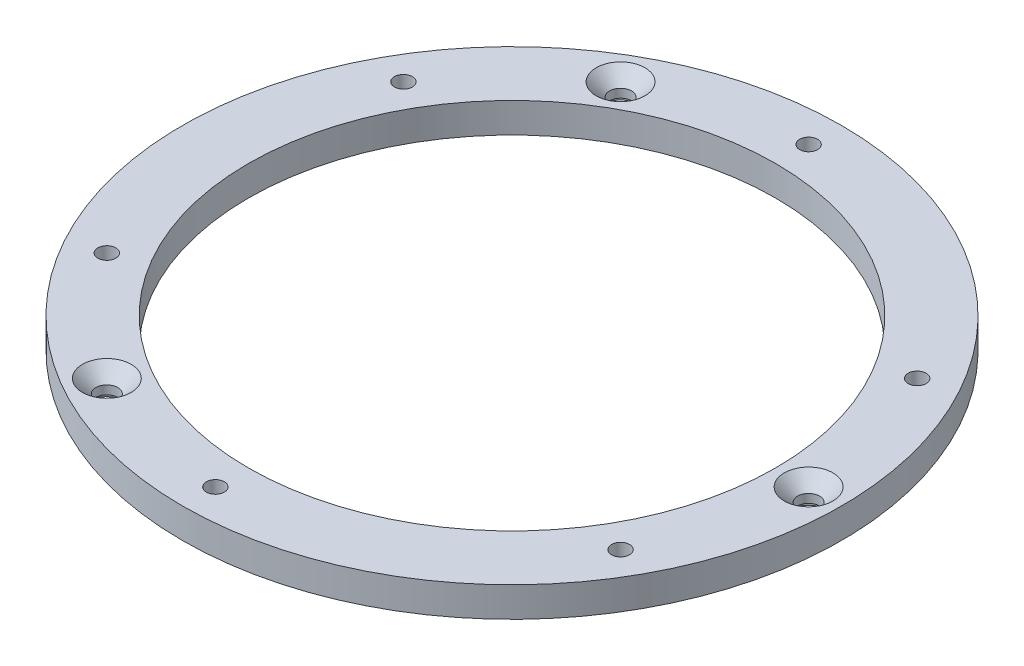
SolidWorks part; units mm, degrees
material "6063-T6"
ref_plane "Front Plane" through (0, 0, 0) normal (0, 0, 1) x (1, 0, 0)
ref_plane "Top Plane" through (0, 0, 0) normal (0, 1, 0) x (1, 0, 0)
ref_plane "Right Plane" through (0, 0, 0) normal (1, 0, 0) x (0, 0, -1)
sketch "Sketch1" plane through (0, 0, 0) normal (0, 1, 0) x (1, 0, 0)
  circle A0 centre (0, 0) radius 132
  circle A1 centre (0, 0) radius 165
  dimension "D1" = 264
  dimension "D2" = 33
extrude "Boss-Extrude1" add sketch "Sketch1" along normal blind 15
ref_plane "Plane1" through (0, -5, 0) normal (0, -1, 0) x (-1, 0, 0)
hole_wizard "M8 Clearance Hole1" positions "Sketch2" profile "Sketch3" hole size "M8" standard "ISO" end condition through all
sketch "Sketch2" plane through (0, 0, 0) normal (0, -1, 0) x (-1, 0, 0)
  line L0 (0, 0) -> (0, 148.5) construction
  circle A0 centre (0, 0) radius 148.5
  point P0 (0, 148.5)
  dimension "D1" = 297
sketch "Sketch3" plane through (0, 0, -148.5) normal (1, 0, 0) x (0, 0, -1)
  line L0 (0, 0) -> (0, 15)
  line L1 (0, 15) -> (4.5, 15)
  line L2 (4.5, 15) -> (4.5, 0)
  line L5 (4.5, 0) -> (0, 0)
  line L11 (0, -6.35) -> (0, 107.95) construction
  dimension "Thru Hole Dia." = 9
  dimension "Thru Hole Depth" = 15
pattern_circular "CirPattern1" count 6 over 360 about axis through (0, 0, 0) along (0, 1, 0) of "M8 Clearance Hole1"
sketch "Sketch4" plane through (0, 0, 0) normal (0, -1, 0) x (1, 0, 0)
  line L0 (0, 0) -> (0, 148.5) construction
  line L1 (0, 148.5) -> (-128.6048, 74.25) construction
  line L2 (-128.6048, 74.25) -> (0, 0) construction
  line L3 (-82.5, 142.8942) -> (-74.25, 128.6048) construction
  line L4 (-74.25, 128.6048) -> (-66, 114.3154) construction
  line L5 (-66, 114.3154) -> (0, 0) construction
  circle A0 centre (-74.25, 128.6048) radius 10
  circle A1 centre (0, 0) radius 148.5 construction
  circle A2 centre (0, 0) radius 165 construction
  circle A3 centre (0, 0) radius 132 construction
  dimension "D1" = 20
extrude "Cut-Extrude1" cut sketch "Sketch4" against normal blind 4
hole_wizard "CSK for M10 Hex Socket Countersunk Cap Screw1" positions "Sketch7" profile "Sketch8" countersink size "M10" standard "ISO" end condition through all
sketch "Sketch7" plane through (0, 15, 0) normal (0, 1, 0) x (1, 0, 0)
  point P0 (-74.25, -128.6048)
sketch "Sketch8" plane through (-74.25, 15, 128.6048) normal (1, 0, 0) x (0, 0, 1)
  line L0 (0, 0) -> (0, 15)
  line L1 (0, 15) -> (5.5, 15)
  line L2 (5.5, 15) -> (5.5, 6.7)
  line L3 (5.5, 6.7) -> (12.2, 0)
  line L5 (12.2, 0) -> (0, 0)
  line L6 (-5.5, 6.7) -> (-12.2, 0) construction
  line L11 (0, -6.35) -> (0, 107.95) construction
  dimension "Thru Hole Dia." = 11
  dimension "Thru Hole Depth" = 15
  dimension "Near C'Sink Dia." = 24.4
  dimension "Near C'Sink Angle" = 90
pattern_circular "CirPattern2" count 3 over 360 about axis through (0, 0, 0) along (0, 1, 0) of "Cut-Extrude1", "CSK for M10 Hex Socket Countersunk Cap Screw1"
